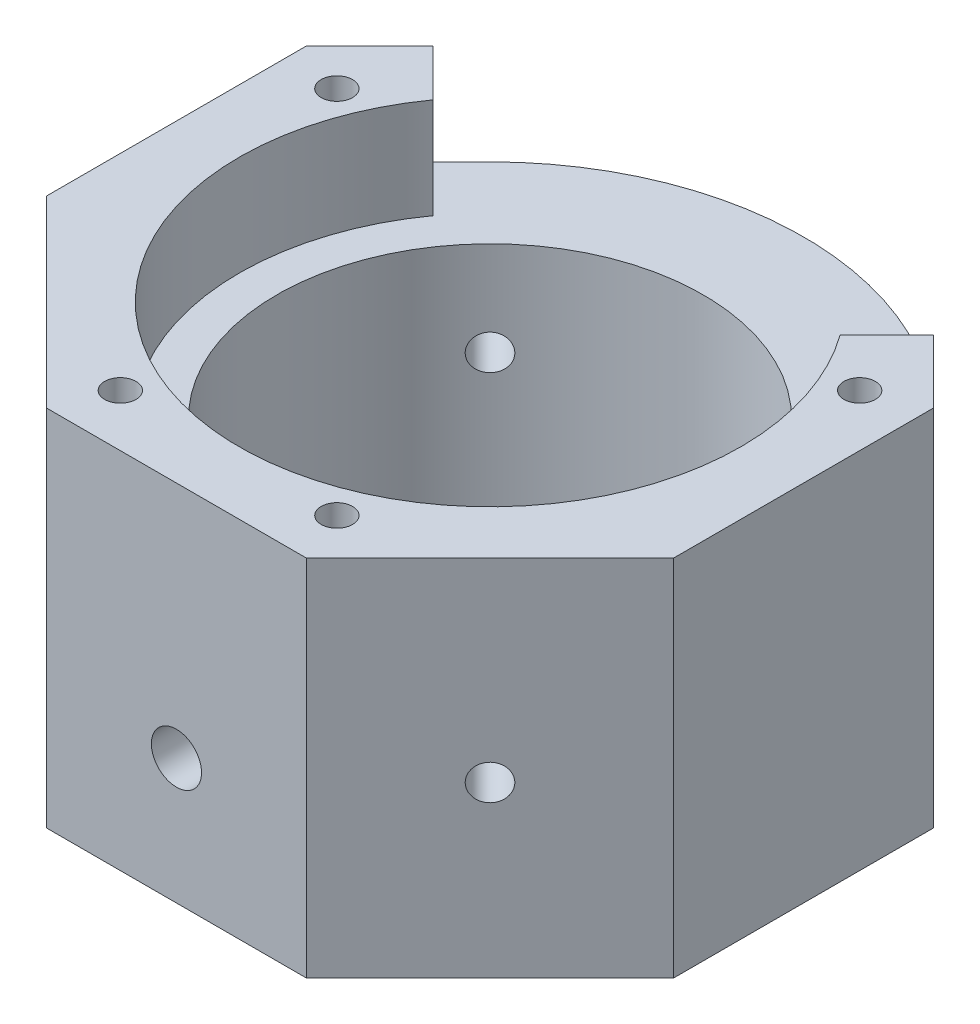
SolidWorks part; units mm, degrees
ref_plane "Front Plane" through (0, 0, 0) normal (0, 0, 1) x (1, 0, 0)
ref_plane "Top Plane" through (0, 0, 0) normal (0, 1, 0) x (1, 0, 0)
ref_plane "Right Plane" through (0, 0, 0) normal (1, 0, 0) x (0, 0, -1)
sketch "Sketch1" plane through (0, 0, 0) normal (0, 1, 0) x (1, 0, 0)
  line L1 (10.3553, 25) -> (-10.3553, 25)
  line L2 (-10.3553, 25) -> (-25, 10.3553)
  line L3 (-25, 10.3553) -> (-25, -10.3553)
  line L4 (-25, -10.3553) -> (-10.3553, -25)
  line L5 (-10.3553, -25) -> (10.3553, -25)
  line L6 (10.3553, -25) -> (25, -10.3553)
  line L7 (25, -10.3553) -> (25, 10.3553)
  line L8 (25, 10.3553) -> (10.3553, 25)
  circle A0 centre (0, 0) radius 25 construction
  circle A1 centre (0, 0) radius 17
  dimension "D2" = 34
  dimension "D1" = 50
extrude "Boss-Extrude1" add sketch "Sketch1" along normal blind 21
sketch "Sketch2" plane through (0, 21, 0) normal (0, 1, 0) x (1, 0, 0)
  line L8 (25, 10.3553) -> (10.3553, 25)
  line L9 (10.3553, 25) -> (-10.3553, 25)
  line L10 (-10.3553, 25) -> (-25, 10.3553)
  line L11 (-25, 10.3553) -> (-25, -10.3553)
  line L12 (-25, -10.3553) -> (-10.3553, -25)
  line L13 (-10.3553, -25) -> (10.3553, -25)
  line L14 (10.3553, -25) -> (25, -10.3553)
  line L15 (25, -10.3553) -> (25, 10.3553)
  line L16 (25, 10.3553) -> (10.3553, 25)
  line L17 (10.3553, 25) -> (-10.3553, 25)
  line L18 (-10.3553, 25) -> (-25, 10.3553)
  line L19 (-25, 10.3553) -> (-25, -10.3553)
  line L20 (-25, -10.3553) -> (-10.3553, -25)
  line L21 (-10.3553, -25) -> (10.3553, -25)
  line L22 (10.3553, -25) -> (25, -10.3553)
  line L23 (25, -10.3553) -> (25, 10.3553)
  circle A3 centre (0, 0) radius 20
  circle A4 centre (0, 0) radius 17 construction
  dimension "D2" = 3
  dimension "D1" = 0
extrude "Boss-Extrude2" add sketch "Sketch2" along normal blind 8
sketch "Sketch6" plane through (0, 29, 0) normal (0, 1, 0) x (1, 0, 0)
  line L0 (0, 0) -> (-17.6777, 17.6777) construction
  line L1 (-10.3553, 25) -> (-25, 10.3553) construction
  line L2 (-19.9404, 15.4149) -> (-16.2227, 11.6972)
  line L3 (-16.2227, 11.6972) -> (16.2227, 11.6972)
  line L4 (16.2227, 11.6972) -> (19.9404, 15.4149)
  line L5 (25, 10.3553) -> (10.3553, 25) construction
  line L6 (19.9404, 15.4149) -> (10.3553, 25)
  line L7 (10.3553, 25) -> (-10.3553, 25)
  line L8 (-10.3553, 25) -> (-19.9404, 15.4149)
  circle A0 centre (0, 0) radius 20 construction
  dimension "D1" = 3.2
extrude "Cut-Extrude3" cut sketch "Sketch6" against normal up to surface (8 mm away) up to face at (0, 21, 17)
hole_wizard "M3 Tapped Hole1" positions "Sketch11" profile "Sketch12" tap size "M3" standard "DIN"
sketch "Sketch11" plane through (0, 29, 0) normal (0, 1, 0) x (1, 0, 0)
  line L0 (20.8425, 8.6333) -> (25, 10.3553) construction
  line L2 (20.8425, 8.6333) -> (0, 0) construction
  line L4 (0, 0) -> (-20.8425, 8.6333) construction
  line L5 (-20.8425, 8.6333) -> (-25, 10.3553) construction
  line L6 (0, 0) -> (-8.6333, -20.8425) construction
  line L7 (-8.6333, -20.8425) -> (-10.3553, -25) construction
  line L9 (0, 0) -> (8.6333, -20.8425) construction
  line L10 (8.6333, -20.8425) -> (10.3553, -25) construction
  point P0 (20.8425, 8.6333)
  point P17 (-20.8425, 8.6333)
  point P28 (-8.6333, -20.8425)
  point P36 (8.6333, -20.8425)
  dimension "D1" = 4.5
sketch "Sketch12" plane through (20.8425, 29, -8.6333) normal (1, 0, 0) x (0, 0, 1)
  line L0 (0, 0) -> (0, 10.7511)
  line L1 (0, 10.7511) -> (1.25, 10)
  line L2 (1.25, 10) -> (1.25, 0)
  line L5 (1.25, 0) -> (0, 0)
  line L10 (0, 10.7511) -> (-1.25, 10) construction
  line L11 (0, -6.35) -> (0, 107.95) construction
  dimension "Tap Drill Dia." = 2.5
  dimension "Tap Drill Depth" = 10
  dimension "Drill Angle" = 118
hole_wizard "#4-40 Tapped Hole1" positions "Sketch13" profile "Sketch14" tap size "#4-40" standard "ANSI Inch"
sketch "Sketch13" plane through (0, 0, 0) normal (0, -1, 0) x (-1, 0, 0)
  line L1 (-15, -15) -> (15, -15) construction
  line L2 (-15, -15) -> (-15, 15) construction
  line L3 (-15, 15) -> (15, 15) construction
  line L4 (15, -15) -> (15, 15) construction
  line L5 (-15, -15) -> (15, 15) construction
  line L6 (-15, 15) -> (15, -15) construction
  point P0 (-15, 15)
  point P2 (15, 15)
  point P4 (-15, -15)
  point P6 (15, -15)
  dimension "D1" = 30
sketch "Sketch14" plane through (15, 0, -15) normal (1, 0, 0) x (0, 0, -1)
  line L0 (0, 0) -> (0, 5.6792)
  line L1 (0, 5.6792) -> (1.1303, 5)
  line L2 (1.1303, 5) -> (1.1303, 0)
  line L5 (1.1303, 0) -> (0, 0)
  line L10 (0, 5.6792) -> (-1.1303, 5) construction
  line L11 (0, -6.35) -> (0, 107.95) construction
  dimension "Tap Drill Dia." = 2.2606
  dimension "Tap Drill Depth" = 5
  dimension "Drill Angle" = 118
cosmetic thread "Hole Thread1" parameters "D1"=5, "D2"=2.8448
cosmetic thread "Hole Thread2" parameters "D1"=5, "D2"=2.8448
cosmetic thread "Hole Thread3" parameters "D1"=5, "D2"=2.8448
cosmetic thread "Hole Thread4" parameters "D1"=5, "D2"=2.8448
hole_wizard "M3x0.2 Tapped Hole1" positions "Sketch16" profile "Sketch17" tap size "M3x0.2" standard "DIN" end condition through all
sketch "Sketch16" plane through (17.6777, 0, -17.6777) normal (0.7071, 0, -0.7071) x (-0.7071, 0, -0.7071)
  line L0 (-10.3553, 0) -> (10.3553, 0) construction
  point P0 (0, 11)
  dimension "D1" = 11
sketch "Sketch17" plane through (17.6777, 11, -17.6777) normal (0, 1, 0) x (-0.7071, 0, -0.7071)
  line L0 (0, 0) -> (0, 60.3553)
  line L1 (0, 60.3553) -> (1.4, 60.3553)
  line L2 (1.4, 60.3553) -> (1.4, 0)
  line L5 (1.4, 0) -> (0, 0)
  line L11 (0, -6.35) -> (0, 107.95) construction
  dimension "Thru Tap Drill Dia." = 2.8
  dimension "Thru Tap Drill Depth" = 60.3553
cosmetic thread "Hole Thread5" parameters "D2"=3
hole_wizard "M3x0.2 Tapped Hole2" positions "Sketch18" profile "Sketch19" tap size "M3x0.2" standard "DIN" end condition through all
sketch "Sketch18" plane through (-17.6777, 0, -17.6777) normal (-0.7071, 0, -0.7071) x (-0.7071, 0, 0.7071)
  line L0 (-10.3553, 0) -> (10.3553, 0) construction
  point P0 (0, 13.5)
  dimension "D1" = 13.5
sketch "Sketch19" plane through (-17.6777, 13.5, -17.6777) normal (0, 1, 0) x (-0.7071, 0, 0.7071)
  line L0 (0, 0) -> (0, 60.3553)
  line L1 (0, 60.3553) -> (1.4, 60.3553)
  line L2 (1.4, 60.3553) -> (1.4, 0)
  line L5 (1.4, 0) -> (0, 0)
  line L11 (0, -6.35) -> (0, 107.95) construction
  dimension "Thru Tap Drill Dia." = 2.8
  dimension "Thru Tap Drill Depth" = 60.3553
cosmetic thread "Hole Thread6" parameters "D2"=3
sketch "Sketch20" plane through (0, 0, 25) normal (0, 0, 1) x (1, 0, 0)
  circle A0 centre (0, 10) radius 2
  dimension "D1" = 4
  dimension "D2" = 10
extrude "Cut-Extrude4" cut sketch "Sketch20" against normal up to next
sketch "Sketch22" plane through (0, 29, 0) normal (0, 1, 0) x (1, 0, 0)
  line L7 (10.3553, 25) -> (19.9404, 15.4149) construction
  line L8 (-19.9404, 15.4149) -> (-10.3553, 25) construction
  line L9 (-17.6777, 17.6777) -> (-17.6777, 26.4023)
  line L10 (-17.6777, 26.4023) -> (17.6777, 26.4023)
  line L11 (17.6777, 26.4023) -> (17.6777, 17.6777)
  arc A1 (-17.6777, 17.6777) -> (17.6777, 17.6777) centre (0, 0) cw
  dimension "D1" = 25
extrude "Cut-Extrude5" cut sketch "Sketch22" against normal blind 12
